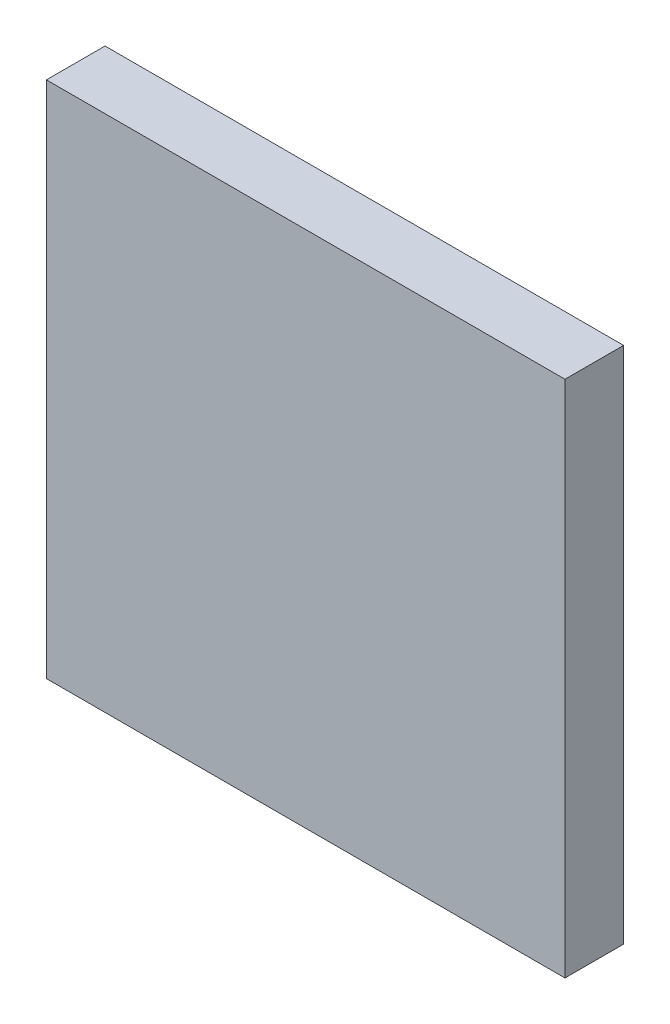
SolidWorks part; units mm, degrees
ref_plane "Front" through (0, 0, 0) normal (0, 0, 1) x (1, 0, 0)
ref_plane "Top" through (0, 0, 0) normal (0, 1, 0) x (1, 0, 0)
ref_plane "Right" through (0, 0, 0) normal (1, 0, 0) x (0, 0, -1)
sketch "Sketch1" plane through (0, 0, 0) normal (0, 0, 1) x (1, 0, 0)
  line L1 (0, 0) -> (23, 0)
  line L2 (0, 0) -> (0, -23)
  line L3 (0, -23) -> (23, -23)
  line L4 (23, 0) -> (23, -23)
  dimension "D1" = 23
  dimension "D2" = 23
extrude "Extrude1" add sketch "Sketch1" along normal blind 2.6
